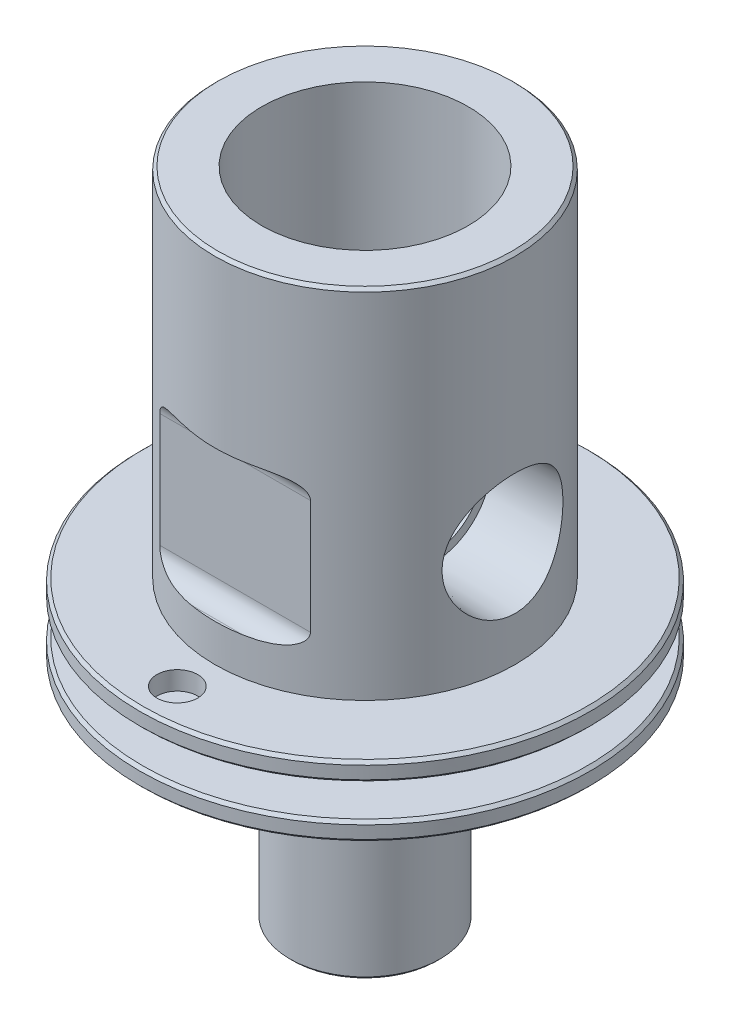
SolidWorks part; units mm, degrees
ref_plane "Front Plane" through (0, 0, 0) normal (0, 0, 1) x (1, 0, 0)
ref_plane "Top Plane" through (0, 0, 0) normal (0, 1, 0) x (1, 0, 0)
ref_plane "Right Plane" through (0, 0, 0) normal (1, 0, 0) x (0, 0, -1)
sketch "Sketch1" plane through (0, 0, 0) normal (1, 0, 0) x (0, 0, -1)
  line L0 (0, 0) -> (0, -110.3122) construction
  line L1 (0, 0) -> (-12.7, 0)
  line L2 (-12.7, 0) -> (-12.7, -30.1625)
  line L3 (-12.7, -30.1625) -> (-19.05, -30.1625)
  line L4 (-19.05, -30.1625) -> (-19.05, -31.7373)
  line L5 (-19.05, -36.1061) -> (-6.35, -36.1061)
  line L6 (-6.35, -36.1061) -> (-6.35, -55.1561)
  line L7 (-6.35, -55.1561) -> (0, -55.1561)
  line L8 (-6.35, -34.5313) -> (-6.35, -31.7373)
  line L9 (-19.05, -31.7373) -> (-6.35, -31.7373)
  line L10 (0, 0) -> (0, -55.1561)
  line L11 (-19.05, -34.5313) -> (-6.35, -34.5313)
  line L12 (-19.05, -34.5313) -> (-19.05, -36.1061)
other "AlignGroup1" parameters "D1"=24.6455, "D2"=9.8005, "D3"=13.3316, "D4"=24.6455, "D5"=13.3316, "D6"=6.35, "D7"=19.05, "D8"=19.05, "D9"=12.7
revolve "Revolve1" add sketch "Sketch1" angle 360 about L0
ref_plane "Plane1" through (12.7, 0, 0) normal (1, 0, 0) x (0, 0, -1)
hole_wizard "1/8 NPT Tapped Hole1" positions "Sketch4" profile "Sketch5" size "1/8" standard "Ansi Inch"
sketch "Sketch4" plane through (12.7, 0, 0) normal (1, 0, 0) x (0, 0, -1)
  line L1 (19.05, -30.1625) -> (-19.05, -30.1625) construction
  point P0 (0, -21.2725)
  dimension "D1" = 8.89
sketch "Sketch5" plane through (12.7, -21.2725, 0) normal (0, 1, 0) x (0, 0, -1)
  line L0 (0, 0) -> (0, 14.1667)
  line L1 (4.2164, 11.6332) -> (0, 14.1667)
  line L2 (-4.2164, 11.6332) -> (0, 14.1667) construction
  line L3 (4.2164, 11.6332) -> (4.2164, 6.9342)
  line L4 (4.2164, 6.9342) -> (4.9362, 6.9342)
  line L5 (4.9362, 6.9342) -> (5.1438, 0)
  line L6 (-4.9362, 6.9342) -> (-5.1438, 0) construction
  line L7 (5.1438, 0) -> (0, 0)
  line L8 (0, -6.35) -> (0, 107.95) construction
  line L11 (-4.2164, 6.9342) -> (-4.9362, 6.9342) construction
  dimension "Tap Drill Dia." = 8.4328
  dimension "Tap Drill Depth" = 11.6332
  dimension "Thread Dia." = 10.2876
  dimension "Thread Angle" = 3.43
  dimension "Thread Depth" = 6.9342
  dimension "Drill Angle" = 118
hole_wizard "3/4-16 Tapped Hole1" positions "Sketch7" profile "Sketch8" tap size "3/4-16" standard "Ansi Inch"
sketch "Sketch7" plane through (0, 0, 0) normal (0, 1, 0) x (-1, 0, 0)
  point P0 (0, 0)
sketch "Sketch8" plane through (0, 0, 0) normal (1, 0, 0) x (0, 0, 1)
  line L0 (0, 0) -> (0, 21.2535)
  line L1 (0, 21.2535) -> (8.7312, 12.5222)
  line L2 (8.7312, 12.5222) -> (8.7312, 0)
  line L5 (8.7312, 0) -> (0, 0)
  line L10 (0, 21.2535) -> (-8.7313, 12.5222) construction
  line L11 (0, -6.35) -> (0, 107.95) construction
  dimension "Tap Drill Dia." = 17.4625
  dimension "Tap Drill Depth" = 12.5222
  dimension "Drill Angle" = 90
cosmetic thread "Hole Thread1" parameters "D1"=4.572, "D2"=19.05
sketch "Sketch9" plane through (0, -55.1561, 0) normal (0, -1, 0) x (1, 0, 0)
  circle A0 centre (0, 0) radius 4.7625
  dimension "D1" = 9.525
extrude "Thru hole" cut sketch "Sketch9" against normal through all
sketch "Sketch10" plane through (0, 0, 0) normal (1, 0, 0) x (0, 0, -1)
  line L0 (-12.7, 0) -> (-12.7, -30.1625) construction
  line L1 (-12.7, -14.2875) -> (-12.5095, -14.2875)
  line L2 (-12.7, -14.2875) -> (-12.7, -26.9875)
  line L3 (-12.7, -26.9875) -> (-12.5095, -26.9875)
  line L4 (-10.9855, -15.8115) -> (-10.9855, -25.4635)
  line L5 (0, 0) -> (0, -54.7172) construction
  line L6 (10.9855, -15.8115) -> (10.9855, -25.4635)
  line L7 (12.7, -26.9875) -> (12.5095, -26.9875)
  line L8 (12.7, -14.2875) -> (12.7, -26.9875)
  line L9 (12.7, -14.2875) -> (12.5095, -14.2875)
  line L10 (19.05, -30.1625) -> (-19.05, -30.1625) construction
  arc A0 (-12.5095, -14.2875) -> (-10.9855, -15.8115) centre (-12.5095, -15.8115) cw
  arc A1 (-12.5095, -26.9875) -> (-10.9855, -25.4635) centre (-12.5095, -25.4635) ccw
  arc A2 (10.9855, -25.4635) -> (12.5095, -26.9875) centre (12.5095, -25.4635) ccw
  arc A3 (10.9855, -15.8115) -> (12.5095, -14.2875) centre (12.5095, -15.8115) cw
  point P17 (-10.9855, -14.2875)
  point P20 (-10.9855, -26.9875)
  point P23 (10.9855, -26.9875)
  point P26 (10.9855, -14.2875)
  dimension "D4" = 1.524
  dimension "D1" = 21.971
  dimension "D2" = 12.7
  dimension "D3" = 3.175
extrude "Wrench flats 7/8\"" cut sketch "Sketch10" against normal mid plane 25.4
chamfer "Break all edges" distance 0.254 angle 45 7 edges at (0, -34.5313, 19.05) (0, -31.7373, 19.05) (0, -55.1561, -4.7625) (0, -55.1561, 6.35) (0, -36.1061, 19.05) (0, -30.1625, 19.05) (0, 0, 12.7)
hole_wizard "#8-32 Tapped Hole1" positions "Sketch12" profile "Sketch11" tap size "#8-32" standard "Ansi Inch"
sketch "Sketch12" plane through (0, -30.1625, 0) normal (0, 1, 0) x (-1, 0, 0)
  point P0 (0, 15.875)
  dimension "D1" = 15.875
sketch "Sketch11" plane through (0, -30.1625, 15.875) normal (1, 0, 0) x (0, 0, 1)
  line L0 (0, 0) -> (0, 6.096)
  line L1 (0, 6.096) -> (1.7272, 4.3688)
  line L2 (1.7272, 4.3688) -> (1.7272, 0)
  line L5 (1.7272, 0) -> (0, 0)
  line L10 (0, 6.096) -> (-1.7272, 4.3688) construction
  line L11 (0, -6.35) -> (0, 107.95) construction
  dimension "Tap Drill Dia." = 3.4544
  dimension "Tap Drill Depth" = 4.3688
  dimension "Drill Angle" = 90
cosmetic thread "Hole Thread2" parameters "D1"=1.5748, "D2"=4.1656
